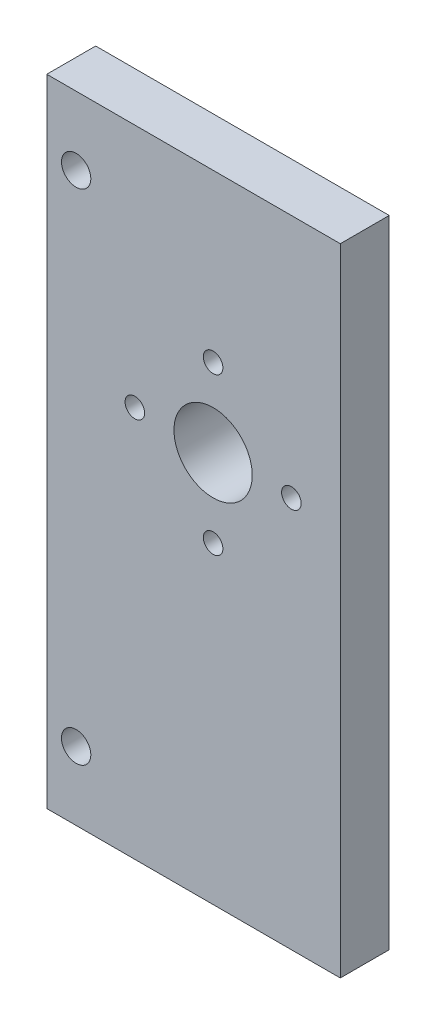
SolidWorks part; units mm, degrees
ref_plane "Plan de face" through (0, 0, 0) normal (0, 0, 1) x (1, 0, 0)
ref_plane "Plan de dessus" through (0, 0, 0) normal (0, 1, 0) x (1, 0, 0)
ref_plane "Plan de droite" through (0, 0, 0) normal (1, 0, 0) x (0, 0, -1)
sketch "Esquisse1" plane through (0, 0, 0) normal (0, 0, 1) x (1, 0, 0)
  line L0 (25.3646, -115.6707) -> (25.3646, -50.6707)
  line L1 (55.3646, -50.6707) -> (25.3646, -50.6707)
  line L2 (55.3646, -50.6707) -> (55.3646, -115.6707)
  line L3 (55.3646, -115.6707) -> (25.3646, -115.6707)
  line L4 (28.3646, -46.6881) -> (28.3646, -124.8997) construction
  circle A0 centre (28.3646, -57.6707) radius 1.5
  circle A1 centre (28.3646, -108.6707) radius 1.5
  circle A2 centre (34.3646, -75.6707) radius 1
  circle A3 centre (42.3646, -67.6707) radius 1
  circle A4 centre (50.3646, -75.6707) radius 1
  circle A5 centre (42.3646, -83.6707) radius 1
  circle A7 centre (42.3646, -75.6707) radius 4
  dimension "D3" = 30
  dimension "D11" = 25
  dimension "D12" = 3
  dimension "D10" = 13
  dimension "D13" = 3
  dimension "D14" = 3
  dimension "D16" = 7
  dimension "D6" = 2
  dimension "D7" = 2
  dimension "D8" = 2
  dimension "D9" = 2
  dimension "D4" = 8
  dimension "D15" = 7
  dimension "D1" = 65
  dimension "D2" = 65
  dimension "D5" = 30
extrude "Boss.-Extru.1" add sketch "Esquisse1" along normal blind 6
sketch "Esquisse5" plane through (0, 0, 0) normal (0, 0, -1) x (-1, 0, 0)
  line L1 (-55.3646, -50.6707) -> (-25.3646, -50.6707)
  line L2 (-55.3646, -50.6707) -> (-55.3646, -115.6707)
  line L3 (-55.3646, -115.6707) -> (-25.3646, -115.6707)
  line L4 (-25.3646, -50.6707) -> (-25.3646, -115.6707)
  circle A0 centre (-42.3646, -75.6707) radius 10.5
  dimension "D1" = 21
extrude "Enlèv. mat.-Extru.4" cut sketch "Esquisse5" against normal blind 1
